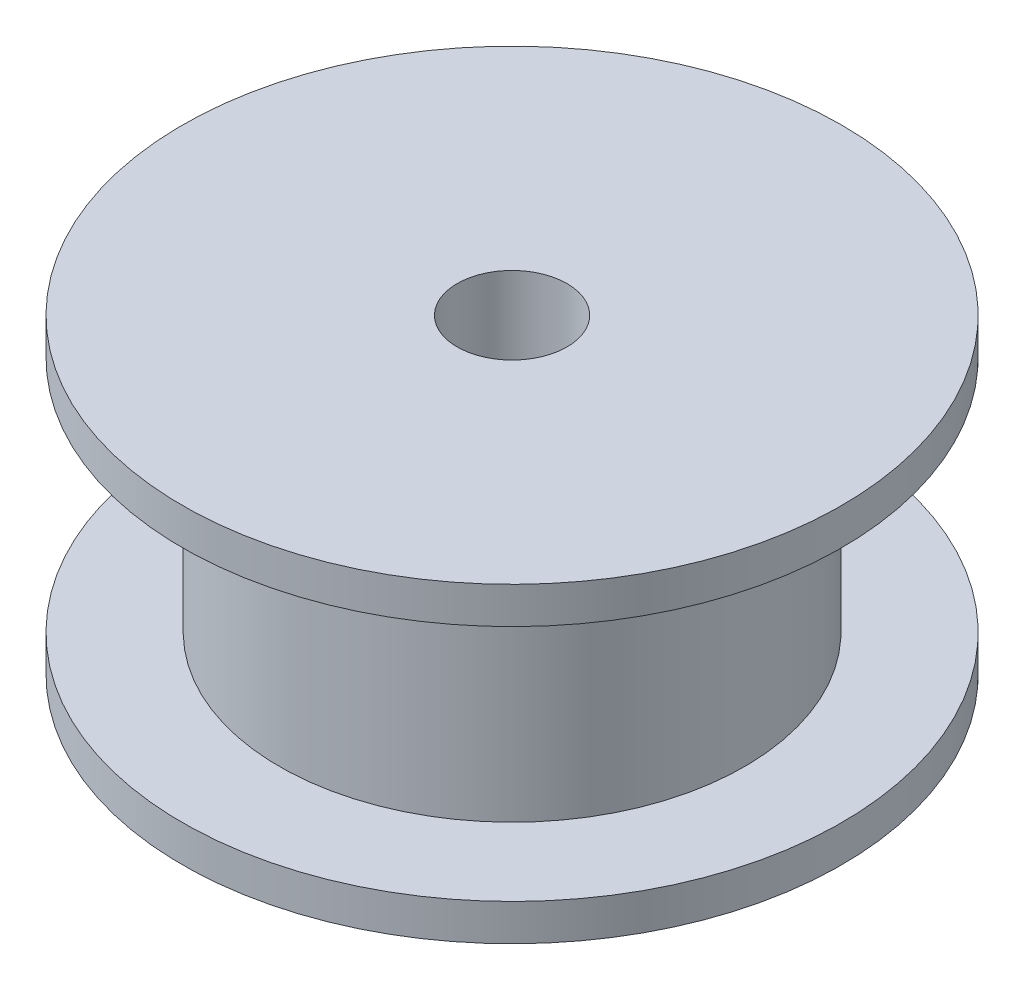
SolidWorks part; units mm, degrees
material "AISI 1020"
ref_plane "Front" through (0, 0, 0) normal (0, 0, 1) x (1, 0, 0)
ref_plane "Top" through (0, 0, 0) normal (0, 1, 0) x (1, 0, 0)
ref_plane "Right" through (0, 0, 0) normal (1, 0, 0) x (0, 0, -1)
sketch "Esboço1" plane through (0, 0, 0) normal (0, 0, 1) x (1, 0, 0)
  line L0 (1.5, 0) -> (9, 0)
  line L1 (9, 0) -> (9, 1)
  line L2 (9, 1) -> (6.35, 1)
  line L3 (6.35, 1) -> (6.35, 7.5)
  line L4 (6.35, 7.5) -> (9, 7.5)
  line L5 (9, 7.5) -> (9, 8.5)
  line L6 (9, 8.5) -> (1.5, 8.5)
  line L7 (1.5, 8.5) -> (1.5, 0)
  line L8 (0, 0) -> (0, 50000) construction
  dimension "D1" = 8.5
  dimension "D2" = 1
  dimension "D3" = 1.5
  dimension "D4" = 9
  dimension "D5" = 12.7
revolve "Revolução1" add sketch "Esboço1" angle 360 about L8
